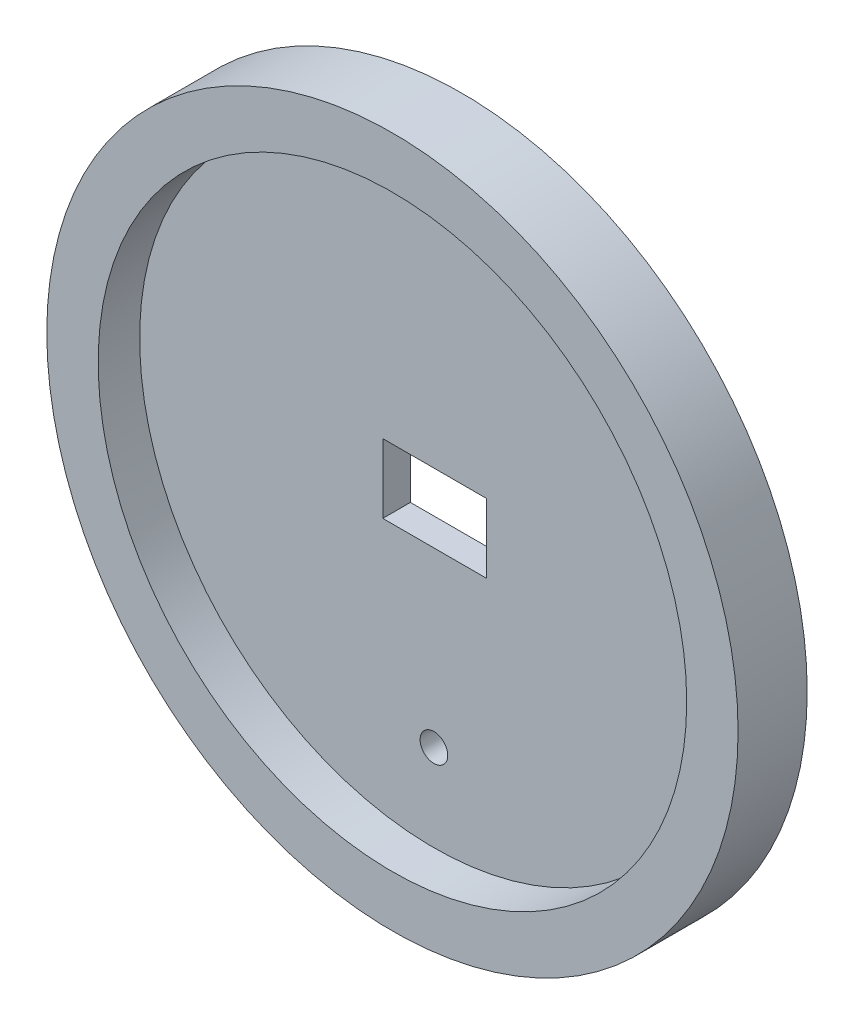
SolidWorks part; units mm, degrees
ref_plane "Plan de face" through (0, 0, 0) normal (0, 0, 1) x (1, 0, 0)
ref_plane "Plan de dessus" through (0, 0, 0) normal (0, 1, 0) x (1, 0, 0)
ref_plane "Plan de droite" through (0, 0, 0) normal (1, 0, 0) x (0, 0, -1)
sketch "Esquisse1" plane through (0, 0, 0) normal (0, 0, 1) x (1, 0, 0)
  line L1 (-3.7, 2.5) -> (3.8, 2.5)
  line L2 (-3.7, 2.5) -> (-3.7, -2.5)
  line L3 (-3.7, -2.5) -> (3.8, -2.5)
  line L4 (3.8, 2.5) -> (3.8, -2.5)
  circle A0 centre (0, 0) radius 25
  circle A1 centre (0, -15) radius 1
  dimension "D5" = 50
  dimension "D6" = 2
  dimension "D1" = 7.5
  dimension "D2" = 5
  dimension "D3" = 2.5
  dimension "D4" = 3.7
  dimension "D7" = 15
extrude "Boss.-Extru.1" add sketch "Esquisse1" along normal blind 5
sketch "Esquisse2" plane through (0, 0, 5) normal (0, 0, 1) x (1, 0, 0)
  circle A0 centre (0, 0) radius 21.2841
extrude "Enlèv. mat.-Extru.1" cut sketch "Esquisse2" against normal blind 3
